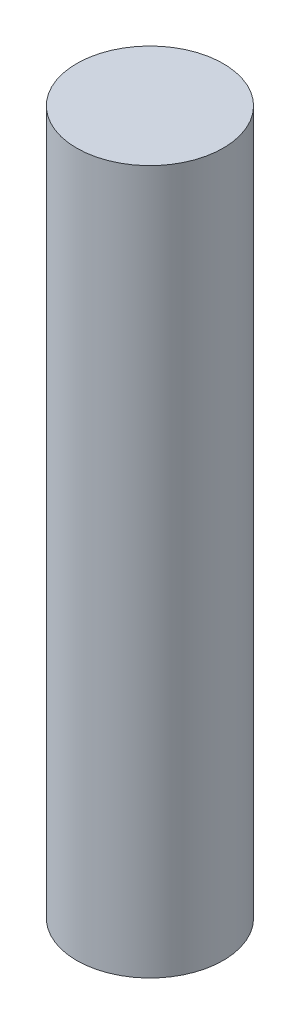
SolidWorks part; units mm, degrees
material "Alloy Steel"
ref_plane "Front Plane" through (0, 0, 0) normal (0, 0, 1) x (1, 0, 0)
ref_plane "Top Plane" through (0, 0, 0) normal (0, 1, 0) x (1, 0, 0)
ref_plane "Right Plane" through (0, 0, 0) normal (1, 0, 0) x (0, 0, -1)
sketch "Sketch1" plane through (0, 0, 0) normal (0, 1, 0) x (1, 0, 0)
  circle A0 centre (0, 0) radius 7.9375
  dimension "D1" = 15.875
extrude "Boss-Extrude1" add sketch "Sketch1" along normal blind 76.2 contours A0
